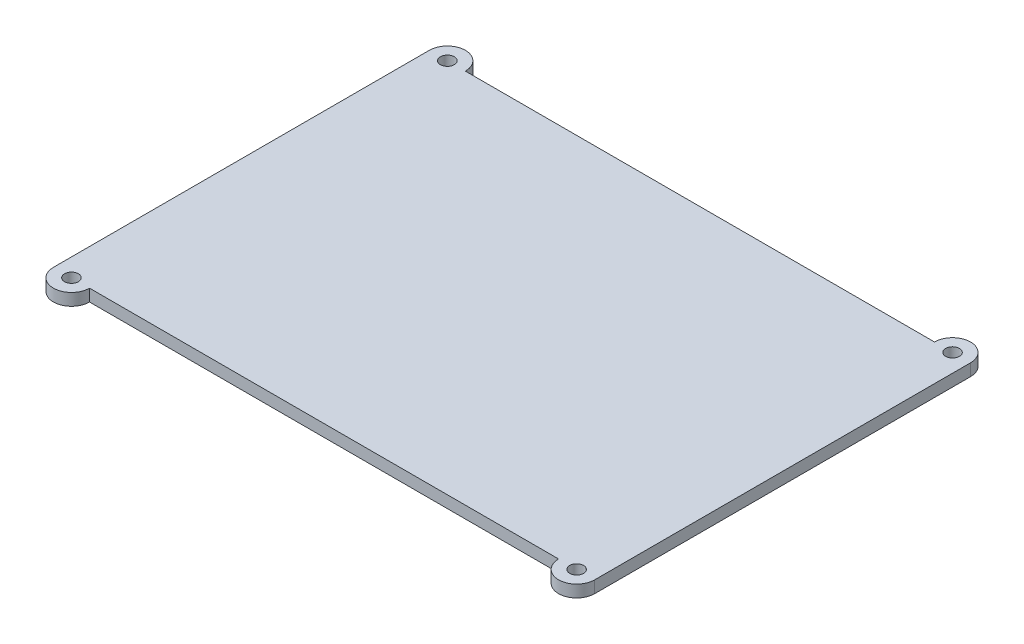
SolidWorks part; units mm, degrees
material "ABS"
ref_plane "Front Plane" through (0, 0, 0) normal (0, 0, 1) x (1, 0, 0)
ref_plane "Top Plane" through (0, 0, 0) normal (0, 1, 0) x (1, 0, 0)
ref_plane "Right Plane" through (0, 0, 0) normal (1, 0, 0) x (0, 0, -1)
sketch "Base" plane through (0, 0, 0) normal (0, 1, 0) x (1, 0, 0)
  line L0 (0, 31.25) -> (90, 31.25) construction
  line L1 (6, 0) -> (84, 0)
  line L2 (0, 0) -> (0, 62.5)
  line L3 (6, 62.5) -> (84, 62.5)
  line L4 (90, 0) -> (90, 62.5)
  line L5 (45, 62.5) -> (45, 0) construction
  arc A0 (0, 62.5) -> (6, 62.5) centre (3, 62.5) cw
  arc A1 (0, 0) -> (6, 0) centre (3, 0) ccw
  arc A2 (90, 0) -> (84, 0) centre (87, 0) cw
  arc A3 (90, 62.5) -> (84, 62.5) centre (87, 62.5) ccw
  point P17 (3, 65.5)
  point P18 (3, -3)
  dimension "D3" = 78
  dimension "D1" = 62.5
  dimension "D2" = 90
  dimension "D4" = 68.5
extrude "Base Extrude" add sketch "Base" along normal blind 2
sketch "Holes" plane through (0, 2, 0) normal (0, 1, 0) x (1, 0, 0)
  line L0 (45, 62.5) -> (45, 0) construction
  line L1 (84, 62.5) -> (6, 62.5) construction
  line L2 (6, 0) -> (84, 0) construction
  line L3 (0, 31.25) -> (90, 31.25) construction
  line L4 (0, 62.5) -> (0, 0) construction
  line L5 (90, 0) -> (90, 62.5) construction
  circle A0 centre (3, 62.5) radius 1.15
  circle A1 centre (87, 62.5) radius 1.15
  circle A2 centre (87, 0) radius 1.15
  circle A3 centre (3, 0) radius 1.15
  dimension "D1" = 2.3
extrude "Holes Cut" cut sketch "Holes" against normal through all
sketch "Inside" plane through (0, 0, 0) normal (0, -1, 0) x (1, 0, 0)
  line L1 (2.25, -60.25) -> (87.75, -60.25)
  line L2 (2.25, -60.25) -> (2.25, -2.25)
  line L3 (2.25, -2.25) -> (87.75, -2.25)
  line L4 (87.75, -60.25) -> (87.75, -2.25)
  line L6 (6, 0) -> (84, 0) construction
  line L7 (0, -62.5) -> (0, 0) construction
  dimension "D1" = 58
  dimension "D2" = 85.5
  dimension "D3" = 2.25
  dimension "D4" = 2.25
extrude "Inside Extrude" add sketch "Inside" along normal blind 2
